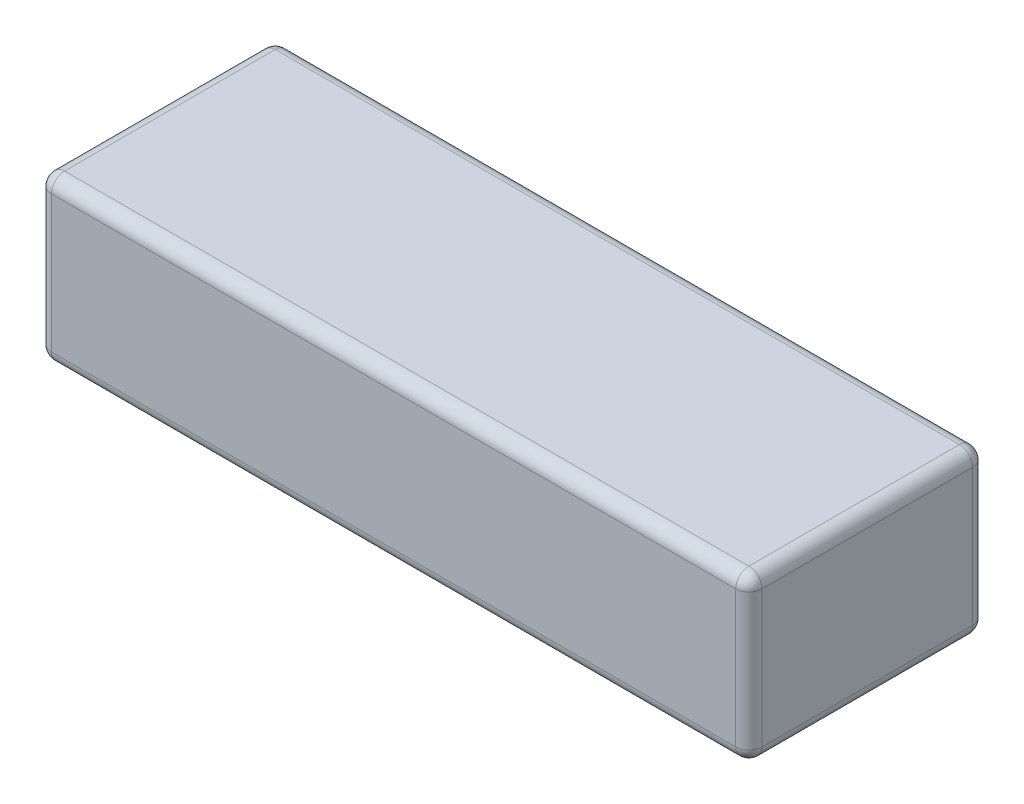
SolidWorks part; units mm, degrees
ref_plane "Front Plane" through (0, 0, 0) normal (0, 0, 1) x (1, 0, 0)
ref_plane "Top Plane" through (0, 0, 0) normal (0, 1, 0) x (1, 0, 0)
ref_plane "Right Plane" through (0, 0, 0) normal (1, 0, 0) x (0, 0, -1)
sketch "Sketch1" plane through (0, 0, 0) normal (0, 1, 0) x (1, 0, 0)
  line L1 (-67.5, -22.5) -> (67.5, -22.5)
  line L2 (-67.5, -22.5) -> (-67.5, 22.5)
  line L3 (-67.5, 22.5) -> (67.5, 22.5)
  line L4 (67.5, -22.5) -> (67.5, 22.5)
  line L5 (-67.5, -22.5) -> (67.5, 22.5) construction
  line L6 (-67.5, 22.5) -> (67.5, -22.5) construction
  point P0 (0, 0)
  dimension "D1" = 135
  dimension "D2" = 45
extrude "Boss-Extrude1" add sketch "Sketch1" along normal blind 31
fillet "Fillet1" radius 2.5 12 edges at (67.5, 15.5, -22.5) (-67.5, 15.5, -22.5) (-67.5, 15.5, 22.5) (67.5, 15.5, 22.5) (0, 31, 22.5) (-67.5, 31, 0) (0, 31, -22.5) (67.5, 31, 0) (0, 0, -22.5) (-67.5, 0, 0) (0, 0, 22.5) (67.5, 0, 0)
